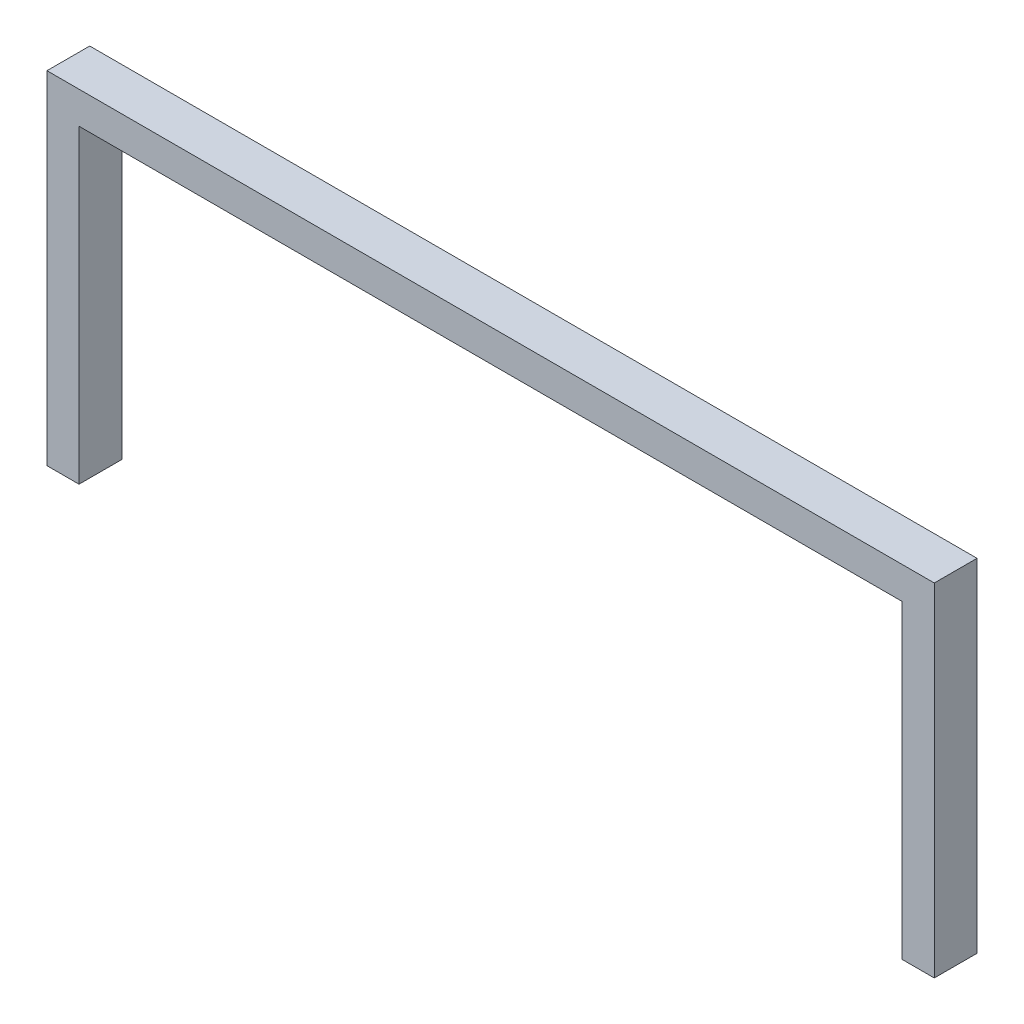
SolidWorks part; units mm, degrees
ref_plane "Front Plane" through (0, 0, 0) normal (0, 0, 1) x (1, 0, 0)
ref_plane "Top Plane" through (0, 0, 0) normal (0, 1, 0) x (1, 0, 0)
ref_plane "Right Plane" through (0, 0, 0) normal (1, 0, 0) x (0, 0, -1)
sketch "Sketch1" plane through (0, 0, 0) normal (0, 0, 1) x (1, 0, 0)
  line L0 (0, 0) -> (-3, 0)
  line L1 (-3, 0) -> (-3, 32)
  line L2 (-3, 32) -> (80, 32)
  line L3 (80, 32) -> (80, 0)
  line L4 (80, 0) -> (77, 0)
  line L5 (77, 0) -> (77, 29)
  line L6 (77, 29) -> (0, 29)
  line L7 (0, 29) -> (0, 0)
  point P6 (0, 0)
  dimension "D1" = 77
  dimension "D2" = 29
  dimension "D3" = 32
  dimension "D4" = 29
  dimension "D5" = 32
  dimension "D6" = 83
  dimension "D7" = 3
  dimension "D8" = 3
  dimension "D9" = 3
  dimension "D10" = 77
  dimension "D11" = 4.2426
  dimension "D12" = 77
  dimension "D13" = 29
extrude "Boss-Extrude1" add sketch "Sketch1" along normal blind 4
